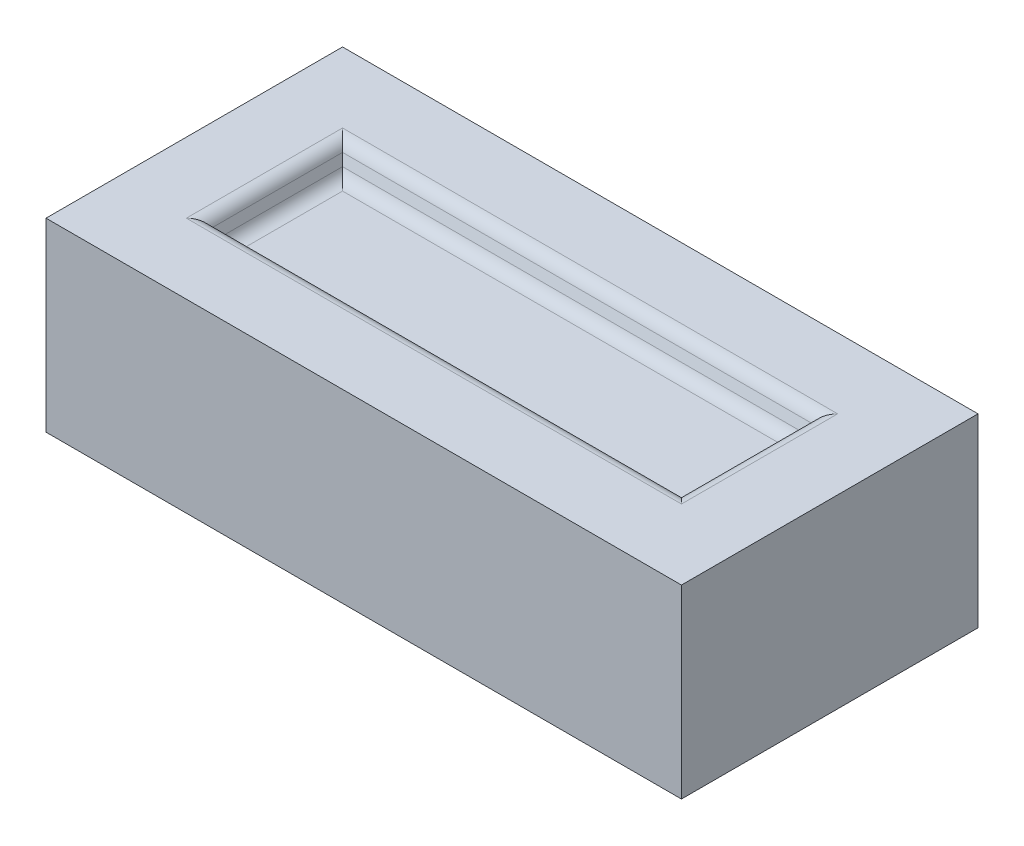
SolidWorks part; units mm, degrees
ref_plane "Front Plane" through (0, 0, 0) normal (0, 0, 1) x (1, 0, 0)
ref_plane "Top Plane" through (0, 0, 0) normal (0, 1, 0) x (1, 0, 0)
ref_plane "Right Plane" through (0, 0, 0) normal (1, 0, 0) x (0, 0, -1)
sketch "Sketch1" plane through (0, 0, 0) normal (0, 1, 0) x (1, 0, 0)
  line L0 (-120, 56) -> (120, -56) construction
  line L1 (-120, 56) -> (120, 56)
  line L2 (-120, 56) -> (-120, -56)
  line L3 (-120, -56) -> (120, -56)
  line L4 (120, 56) -> (120, -56)
  dimension "D1" = 112
  dimension "D2" = 240
extrude "Boss-Extrude1" add sketch "Sketch1" along normal blind 70
sketch "Sketch2" plane through (0, 70, 0) normal (0, 1, 0) x (1, 0, 0)
  line L0 (120, 56) -> (-120, 56) construction
  line L1 (-90, 26) -> (90, 26)
  line L2 (-90, 26) -> (-90, -26)
  line L3 (-90, -26) -> (90, -26)
  line L4 (90, 26) -> (90, -26)
  line L5 (-90, 26) -> (90, -26) construction
  line L6 (-90, -26) -> (90, 26) construction
  line L7 (120, -56) -> (120, 56) construction
  point P0 (0, 0)
  point P6 (0, 26)
  dimension "D1" = 30
  dimension "D2" = 30
extrude "Cut-Extrude1" cut sketch "Sketch2" against normal blind 10 draft 20
ref_plane "Plane1" through (0, 35, 0) normal (0, 1, 0) x (1, 0, 0)
mirror "Mirror1" about plane through (0, 35, 0) normal (0, 1, 0) of "Cut-Extrude1"
fillet "Fillet1" radius 5 16 edges at (0, 10, -22.3603) (-86.3603, 10, 0) (0, 10, 22.3603) (86.3603, 10, 0) (0, 60, 22.3603) (-86.3603, 60, 0) (0, 60, -22.3603) (86.3603, 60, 0) (0, 0, 26) (-90, 0, 0) (0, 0, -26) (90, 0, 0) (0, 70, -26) (-90, 70, 0) (0, 70, 26) (90, 70, 0)
sketch3d "URDF Reference"
  line L0 (0, 0, 0) -> (10, 0, 0) construction
  line L1 (0, 0, 0) -> (0, 0, -10) construction
  point P0 (0, 0, 0)
  point P1 (0, 0, 0)
